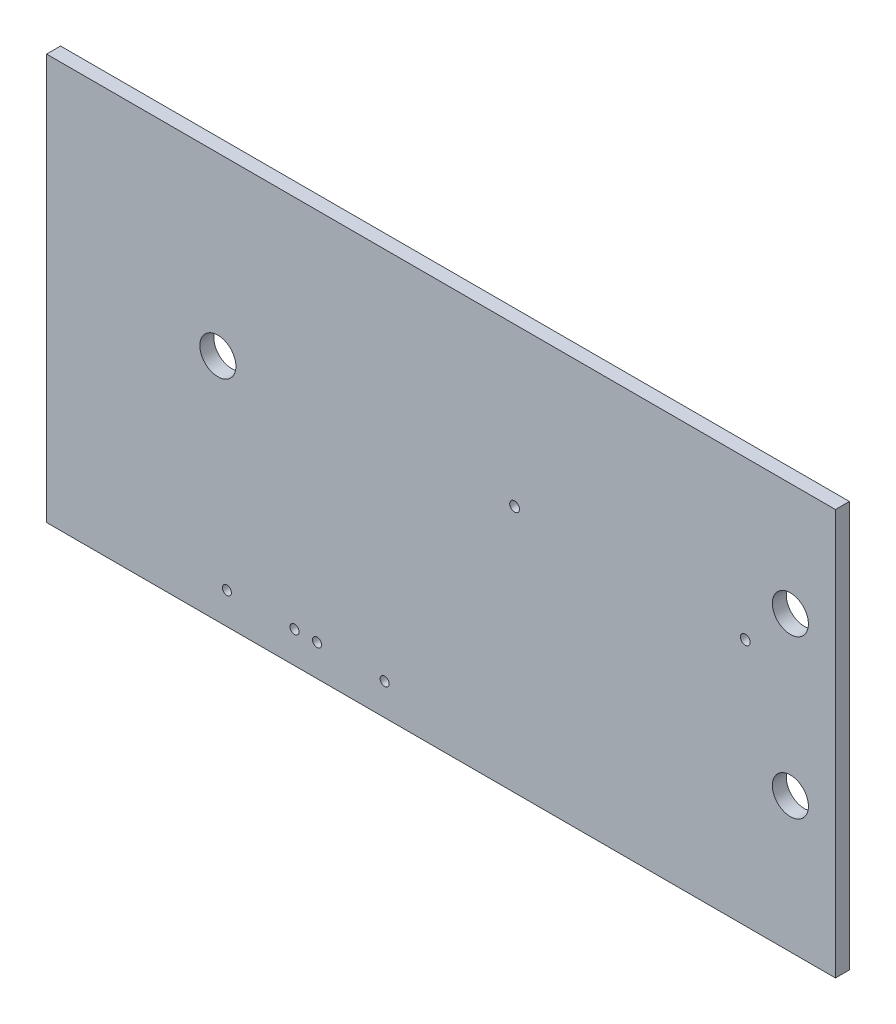
SolidWorks part; units mm, degrees
ref_plane "Front" through (0, 0, 0) normal (0, 0, 1) x (1, 0, 0)
ref_plane "Top" through (0, 0, 0) normal (0, 1, 0) x (1, 0, 0)
ref_plane "Right" through (0, 0, 0) normal (1, 0, 0) x (0, 0, -1)
sketch "Sketch1" plane through (0, 0, 0) normal (0, 0, 1) x (1, 0, 0)
  line L1 (0, 0) -> (88.9, 0)
  line L2 (0, 0) -> (0, -45.72)
  line L3 (0, -45.72) -> (88.9, -45.72)
  line L4 (88.9, 0) -> (88.9, -45.72)
  dimension "D1" = 88.9
  dimension "D2" = 45.72
extrude "board shape -extrude" add sketch "Sketch1" along normal blind 1.5748
sketch "Sketch2" plane through (0, 0, 1.5748) normal (0, 0, 1) x (1, 0, 0)
  line L0 (88.9, -45.72) -> (88.9, 0) construction
  line L1 (0, -45.72) -> (88.9, -45.72) construction
  circle A0 centre (52.74, -17.78) radius 0.55
  circle A1 centre (78.74, -17.78) radius 0.55
  dimension "D1" = 1.1
  dimension "D2" = 1.1
  dimension "D3" = 26
  dimension "D4" = 10.16
  dimension "D5" = 27.94
extrude "mmc mount hole - cut" cut sketch "Sketch2" against normal blind 1.5748
sketch "Sketch4" plane through (0, 0, 1.5748) normal (0, 0, 1) x (1, 0, 0)
  line L0 (0, -45.72) -> (88.9, -45.72) construction
  line L1 (88.9, -45.72) -> (88.9, 0) construction
  circle A0 centre (20.32, -42.164) radius 0.508
  circle A1 centre (27.94, -42.164) radius 0.508
  circle A2 centre (30.48, -42.164) radius 0.508
  circle A3 centre (38.1, -42.164) radius 0.508
  dimension "D1" = 1.016
  dimension "D2" = 1.016
  dimension "D3" = 1.016
  dimension "D4" = 1.016
  dimension "D5" = 3.556
  dimension "D6" = 7.62
  dimension "D7" = 2.54
  dimension "D8" = 7.62
  dimension "D9" = 50.8
extrude "HFBR anchor holes" cut sketch "Sketch4" against normal blind 1.5748
sketch "Sketch5" plane through (0, 0, 1.5748) normal (0, 0, 1) x (1, 0, 0)
  line L0 (0, -45.72) -> (88.9, -45.72) construction
  line L1 (88.9, -45.72) -> (88.9, 0) construction
  circle A0 centre (83.82, -30.48) radius 2.032
  circle A1 centre (83.82, -12.7) radius 2.032
  circle A2 centre (19.304, -19.812) radius 2.032
  dimension "D1" = 15.24
  dimension "D3" = 4.064
  dimension "D4" = 4.064
  dimension "D5" = 4.064
  dimension "D2" = 5.08
  dimension "D6" = 17.78
  dimension "D7" = 64.516
  dimension "D8" = 10.668
extrude "Cut-Extrude3" cut sketch "Sketch5" against normal blind 1.5748
